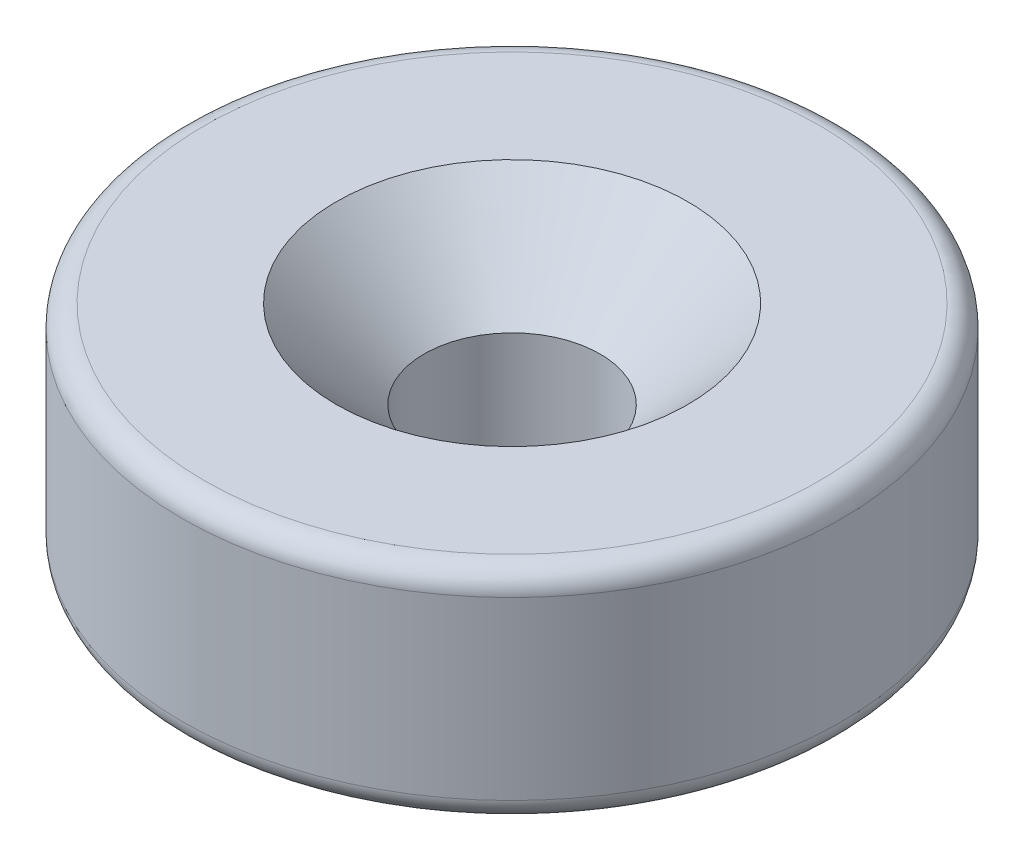
SolidWorks part; units mm, degrees
ref_plane "Front Plane" through (0, 0, 0) normal (0, 0, 1) x (1, 0, 0)
ref_plane "Top Plane" through (0, 0, 0) normal (0, 1, 0) x (1, 0, 0)
ref_plane "Right Plane" through (0, 0, 0) normal (1, 0, 0) x (0, 0, -1)
sketch "Sketch1" plane through (0, 0, 0) normal (0, 1, 0) x (1, 0, 0)
  circle A0 centre (0, 0) radius 7.5
  circle A1 centre (0, 0) radius 2
  dimension "D1" = 15
  dimension "D2" = 4
extrude "Boss-Extrude1" add sketch "Sketch1" along normal mid plane 5
fillet "Fillet1" radius 0.5 2 edges at (0, -2.5, 7.5) (0, 2.5, 7.5)
chamfer "Chamfer1" distance 2 angle 45 1 edges at (0, 2.5, 2)
